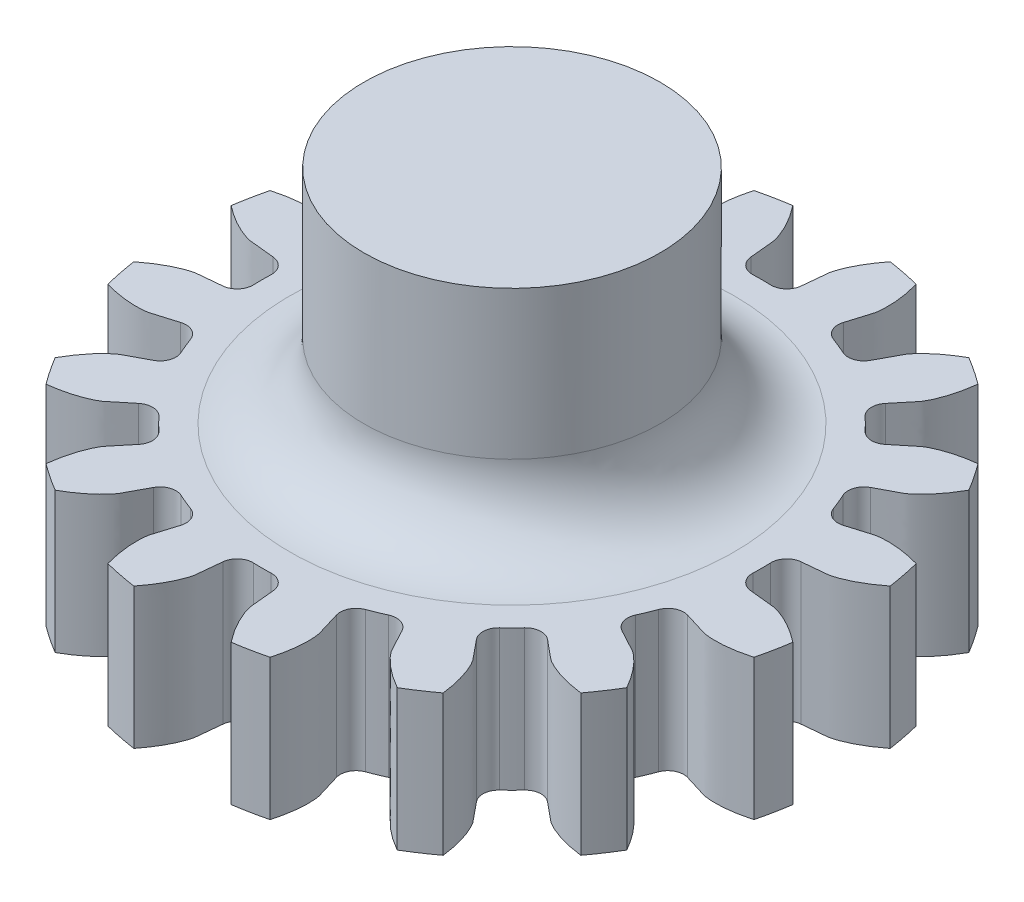
SolidWorks part; units mm, degrees
ref_plane "Front Plane" through (0, 0, 0) normal (0, 0, 1) x (1, 0, 0)
ref_plane "Top Plane" through (0, 0, 0) normal (0, 1, 0) x (1, 0, 0)
ref_plane "Right Plane" through (0, 0, 0) normal (1, 0, 0) x (0, 0, -1)
ref_plane "Plane1" through (0, -3.8, 0) normal (0, -1, 0) x (1, 0, 0)
sketch "Sketch1" plane through (0, -3.8, 0) normal (0, -1, 0) x (1, 0, 0)
  line L0 (1.32, -1.149) -> (-1.32, -1.149)
  arc A0 (-1.32, -1.149) -> (1.32, -1.149) centre (0, 0) cw
  arc A1 (7.1331, -0.679) -> (6.7458, -0.2386) centre (7.1726, -0.2537) cw
  arc A2 (6.7458, -0.2386) -> (6.7458, 0.2386) centre (0, 0) ccw
  arc A3 (6.7458, 0.2386) -> (7.1331, 0.679) centre (7.1726, 0.2537) cw
  arc A4 (8.9035, 1.3146) -> (8.7288, 2.1927) centre (0, 0) ccw
  arc A5 (6.8499, 2.1024) -> (6.3236, 2.3611) centre (6.7237, 2.5105) cw
  arc A6 (6.3236, 2.3611) -> (6.141, 2.8019) centre (0, 0) ccw
  arc A7 (6.141, 2.8019) -> (6.3303, 3.357) centre (6.5296, 2.9792) cw
  arc A8 (7.7227, 4.6217) -> (7.2253, 5.3661) centre (0, 0) ccw
  arc A9 (5.5239, 4.5638) -> (4.9387, 4.6013) centre (5.2512, 4.8924) cw
  arc A10 (4.9387, 4.6013) -> (4.6013, 4.9387) centre (0, 0) ccw
  arc A11 (4.6013, 4.9387) -> (4.5638, 5.5239) centre (4.8924, 5.2512) cw
  arc A12 (5.3661, 7.2253) -> (4.6217, 7.7227) centre (0, 0) ccw
  arc A13 (3.357, 6.3303) -> (2.8019, 6.141) centre (2.9792, 6.5296) cw
  arc A14 (2.8019, 6.141) -> (2.3611, 6.3236) centre (0, 0) ccw
  arc A15 (2.3611, 6.3236) -> (2.1024, 6.8499) centre (2.5105, 6.7237) cw
  arc A16 (2.1927, 8.7288) -> (1.3146, 8.9035) centre (0, 0) ccw
  arc A17 (0.679, 7.1331) -> (0.2386, 6.7458) centre (0.2537, 7.1726) cw
  arc A18 (0.2386, 6.7458) -> (-0.2386, 6.7458) centre (0, 0) ccw
  arc A19 (-0.2386, 6.7458) -> (-0.679, 7.1331) centre (-0.2537, 7.1726) cw
  arc A20 (-1.3146, 8.9035) -> (-2.1927, 8.7288) centre (0, 0) ccw
  arc A21 (-2.1024, 6.8499) -> (-2.3611, 6.3236) centre (-2.5105, 6.7237) cw
  arc A22 (-2.3611, 6.3236) -> (-2.8019, 6.141) centre (0, 0) ccw
  arc A23 (-2.8019, 6.141) -> (-3.357, 6.3303) centre (-2.9792, 6.5296) cw
  arc A24 (-4.6217, 7.7227) -> (-5.3661, 7.2253) centre (0, 0) ccw
  arc A25 (-4.5638, 5.5239) -> (-4.6013, 4.9387) centre (-4.8924, 5.2512) cw
  arc A26 (-4.6013, 4.9387) -> (-4.9387, 4.6013) centre (0, 0) ccw
  arc A27 (-4.9387, 4.6013) -> (-5.5239, 4.5638) centre (-5.2512, 4.8924) cw
  arc A28 (-7.2253, 5.3661) -> (-7.7227, 4.6217) centre (0, 0) ccw
  arc A29 (-6.3303, 3.357) -> (-6.141, 2.8019) centre (-6.5296, 2.9792) cw
  arc A30 (-6.141, 2.8019) -> (-6.3236, 2.3611) centre (0, 0) ccw
  arc A31 (-6.3236, 2.3611) -> (-6.8499, 2.1024) centre (-6.7237, 2.5105) cw
  arc A32 (-8.7288, 2.1927) -> (-8.9035, 1.3146) centre (0, 0) ccw
  arc A33 (-7.1331, 0.679) -> (-6.7458, 0.2386) centre (-7.1726, 0.2537) cw
  arc A34 (-6.7458, 0.2386) -> (-6.7458, -0.2386) centre (0, 0) ccw
  arc A35 (-6.7458, -0.2386) -> (-7.1331, -0.679) centre (-7.1726, -0.2537) cw
  arc A36 (-8.9035, -1.3146) -> (-8.7288, -2.1927) centre (0, 0) ccw
  arc A37 (-6.8499, -2.1024) -> (-6.3236, -2.3611) centre (-6.7237, -2.5105) cw
  arc A38 (-6.3236, -2.3611) -> (-6.141, -2.8019) centre (0, 0) ccw
  arc A39 (-6.141, -2.8019) -> (-6.3303, -3.357) centre (-6.5296, -2.9792) cw
  arc A40 (-7.7227, -4.6217) -> (-7.2253, -5.3661) centre (0, 0) ccw
  arc A41 (-5.5239, -4.5638) -> (-4.9387, -4.6013) centre (-5.2512, -4.8924) cw
  arc A42 (-4.9387, -4.6013) -> (-4.6013, -4.9387) centre (0, 0) ccw
  arc A43 (-4.6013, -4.9387) -> (-4.5638, -5.5239) centre (-4.8924, -5.2512) cw
  arc A44 (-5.3661, -7.2253) -> (-4.6217, -7.7227) centre (0, 0) ccw
  arc A45 (-3.357, -6.3303) -> (-2.8019, -6.141) centre (-2.9792, -6.5296) cw
  arc A46 (-2.8019, -6.141) -> (-2.3611, -6.3236) centre (0, 0) ccw
  arc A47 (-2.3611, -6.3236) -> (-2.1024, -6.8499) centre (-2.5105, -6.7237) cw
  arc A48 (-2.1927, -8.7288) -> (-1.3146, -8.9035) centre (0, 0) ccw
  arc A49 (-0.679, -7.1331) -> (-0.2386, -6.7458) centre (-0.2537, -7.1726) cw
  arc A50 (-0.2386, -6.7458) -> (0.2386, -6.7458) centre (0, 0) ccw
  arc A51 (0.2386, -6.7458) -> (0.679, -7.1331) centre (0.2537, -7.1726) cw
  arc A52 (1.3146, -8.9035) -> (2.1927, -8.7288) centre (0, 0) ccw
  arc A53 (2.1024, -6.8499) -> (2.3611, -6.3236) centre (2.5105, -6.7237) cw
  arc A54 (2.3611, -6.3236) -> (2.8019, -6.141) centre (0, 0) ccw
  arc A55 (2.8019, -6.141) -> (3.357, -6.3303) centre (2.9792, -6.5296) cw
  arc A56 (4.6217, -7.7227) -> (5.3661, -7.2253) centre (0, 0) ccw
  arc A57 (4.5638, -5.5239) -> (4.6013, -4.9387) centre (4.8924, -5.2512) cw
  arc A58 (4.6013, -4.9387) -> (4.9387, -4.6013) centre (0, 0) ccw
  arc A59 (4.9387, -4.6013) -> (5.5239, -4.5638) centre (5.2512, -4.8924) cw
  arc A60 (7.2253, -5.3661) -> (7.7227, -4.6217) centre (0, 0) ccw
  arc A61 (6.3303, -3.357) -> (6.141, -2.8019) centre (6.5296, -2.9792) cw
  arc A62 (6.141, -2.8019) -> (6.3236, -2.3611) centre (0, 0) ccw
  arc A63 (6.3236, -2.3611) -> (6.8499, -2.1024) centre (6.7237, -2.5105) cw
  arc A64 (8.7288, -2.1927) -> (8.9035, -1.3146) centre (0, 0) ccw
  spline S0 degree 3 poles (7.1331, -0.679) (7.4618, -0.7095) (7.7948, -0.7412) (7.8257, -0.7485) (7.8795, -0.7599) (7.9434, -0.7779) (8.0276, -0.8057) (8.1278, -0.8446) (8.244, -0.8965) (8.3748, -0.963) (8.5191, -1.0456) (8.6757, -1.1461) (8.8054, -1.2381) (8.8825, -1.298) (8.9035, -1.3146) knots 0.061706 0.061706 0.061706 0.061706 0.215819 0.251311 0.29713 0.351345 0.412818 0.480779 0.55466 0.634022 0.718508 0.807827 0.901728 0.93689 0.93689 0.93689 0.93689
  spline S1 degree 3 poles (7.1331, 0.679) (7.4618, 0.7095) (7.7948, 0.7412) (7.8257, 0.7485) (7.8795, 0.7599) (7.9434, 0.7779) (8.0276, 0.8057) (8.1278, 0.8446) (8.244, 0.8965) (8.3748, 0.963) (8.5191, 1.0456) (8.6757, 1.1461) (8.8054, 1.2381) (8.8825, 1.298) (8.9035, 1.3146) knots 0.061706 0.061706 0.061706 0.061706 0.215819 0.251311 0.29713 0.351345 0.412818 0.480779 0.55466 0.634022 0.718508 0.807827 0.901728 0.93689 0.93689 0.93689 0.93689
  spline S2 degree 3 poles (6.8499, 2.1024) (7.1654, 2.2) (7.485, 2.2982) (7.5165, 2.3032) (7.5705, 2.3133) (7.6364, 2.3211) (7.7249, 2.3277) (7.8323, 2.33) (7.9595, 2.3266) (8.1058, 2.3152) (8.2708, 2.2942) (8.4539, 2.2612) (8.6089, 2.2258) (8.7031, 2.2) (8.7288, 2.1927) knots 0.061706 0.061706 0.061706 0.061706 0.215819 0.251311 0.29713 0.351345 0.412818 0.480779 0.55466 0.634022 0.718508 0.807827 0.901728 0.93689 0.93689 0.93689 0.93689
  spline S3 degree 3 poles (6.3303, 3.357) (6.6223, 3.511) (6.9178, 3.6677) (6.9436, 3.6863) (6.9889, 3.7174) (7.041, 3.7585) (7.1083, 3.8164) (7.1859, 3.8907) (7.2734, 3.9831) (7.3688, 4.0946) (7.4705, 4.2261) (7.5767, 4.3789) (7.6613, 4.5136) (7.7096, 4.5984) (7.7227, 4.6217) knots 0.061706 0.061706 0.061706 0.061706 0.215819 0.251311 0.29713 0.351345 0.412818 0.480779 0.55466 0.634022 0.718508 0.807827 0.901728 0.93689 0.93689 0.93689 0.93689
  spline S4 degree 3 poles (5.5239, 4.5638) (5.778, 4.7746) (6.0358, 4.9876) (6.0629, 5.0043) (6.109, 5.0343) (6.1669, 5.0667) (6.2461, 5.1067) (6.3444, 5.15) (6.4633, 5.1955) (6.6028, 5.241) (6.7633, 5.2846) (6.945, 5.3242) (7.1018, 5.3509) (7.1987, 5.363) (7.2253, 5.3661) knots 0.061706 0.061706 0.061706 0.061706 0.215819 0.251311 0.29713 0.351345 0.412818 0.480779 0.55466 0.634022 0.718508 0.807827 0.901728 0.93689 0.93689 0.93689 0.93689
  spline S5 degree 3 poles (4.5638, 5.5239) (4.7746, 5.778) (4.9876, 6.0358) (5.0043, 6.0629) (5.0343, 6.109) (5.0667, 6.1669) (5.1067, 6.2461) (5.15, 6.3444) (5.1955, 6.4633) (5.241, 6.6028) (5.2846, 6.7633) (5.3242, 6.945) (5.3509, 7.1018) (5.363, 7.1987) (5.3661, 7.2253) knots 0.061706 0.061706 0.061706 0.061706 0.215819 0.251311 0.29713 0.351345 0.412818 0.480779 0.55466 0.634022 0.718508 0.807827 0.901728 0.93689 0.93689 0.93689 0.93689
  spline S6 degree 3 poles (3.357, 6.3303) (3.511, 6.6223) (3.6677, 6.9178) (3.6863, 6.9436) (3.7174, 6.9889) (3.7585, 7.041) (3.8164, 7.1083) (3.8907, 7.1859) (3.9831, 7.2734) (4.0946, 7.3688) (4.2261, 7.4705) (4.3789, 7.5767) (4.5136, 7.6613) (4.5984, 7.7096) (4.6217, 7.7227) knots 0.061706 0.061706 0.061706 0.061706 0.215819 0.251311 0.29713 0.351345 0.412818 0.480779 0.55466 0.634022 0.718508 0.807827 0.901728 0.93689 0.93689 0.93689 0.93689
  spline S7 degree 3 poles (2.1024, 6.8499) (2.2, 7.1654) (2.2982, 7.485) (2.3032, 7.5165) (2.3133, 7.5705) (2.3211, 7.6364) (2.3277, 7.7249) (2.33, 7.8323) (2.3266, 7.9595) (2.3152, 8.1058) (2.2942, 8.2708) (2.2612, 8.4539) (2.2258, 8.6089) (2.2, 8.7031) (2.1927, 8.7288) knots 0.061706 0.061706 0.061706 0.061706 0.215819 0.251311 0.29713 0.351345 0.412818 0.480779 0.55466 0.634022 0.718508 0.807827 0.901728 0.93689 0.93689 0.93689 0.93689
  spline S8 degree 3 poles (0.679, 7.1331) (0.7095, 7.4618) (0.7412, 7.7948) (0.7485, 7.8257) (0.7599, 7.8795) (0.7779, 7.9434) (0.8057, 8.0276) (0.8446, 8.1278) (0.8965, 8.244) (0.963, 8.3748) (1.0456, 8.5191) (1.1461, 8.6757) (1.2381, 8.8054) (1.298, 8.8825) (1.3146, 8.9035) knots 0.061706 0.061706 0.061706 0.061706 0.215819 0.251311 0.29713 0.351345 0.412818 0.480779 0.55466 0.634022 0.718508 0.807827 0.901728 0.93689 0.93689 0.93689 0.93689
  spline S9 degree 3 poles (-0.679, 7.1331) (-0.7095, 7.4618) (-0.7412, 7.7948) (-0.7485, 7.8257) (-0.7599, 7.8795) (-0.7779, 7.9434) (-0.8057, 8.0276) (-0.8446, 8.1278) (-0.8965, 8.244) (-0.963, 8.3748) (-1.0456, 8.5191) (-1.1461, 8.6757) (-1.2381, 8.8054) (-1.298, 8.8825) (-1.3146, 8.9035) knots 0.061706 0.061706 0.061706 0.061706 0.215819 0.251311 0.29713 0.351345 0.412818 0.480779 0.55466 0.634022 0.718508 0.807827 0.901728 0.93689 0.93689 0.93689 0.93689
  spline S10 degree 3 poles (-2.1024, 6.8499) (-2.2, 7.1654) (-2.2982, 7.485) (-2.3032, 7.5165) (-2.3133, 7.5705) (-2.3211, 7.6364) (-2.3277, 7.7249) (-2.33, 7.8323) (-2.3266, 7.9595) (-2.3152, 8.1058) (-2.2942, 8.2708) (-2.2612, 8.4539) (-2.2258, 8.6089) (-2.2, 8.7031) (-2.1927, 8.7288) knots 0.061706 0.061706 0.061706 0.061706 0.215819 0.251311 0.29713 0.351345 0.412818 0.480779 0.55466 0.634022 0.718508 0.807827 0.901728 0.93689 0.93689 0.93689 0.93689
  spline S11 degree 3 poles (-3.357, 6.3303) (-3.511, 6.6223) (-3.6677, 6.9178) (-3.6863, 6.9436) (-3.7174, 6.9889) (-3.7585, 7.041) (-3.8164, 7.1083) (-3.8907, 7.1859) (-3.9831, 7.2734) (-4.0946, 7.3688) (-4.2261, 7.4705) (-4.3789, 7.5767) (-4.5136, 7.6613) (-4.5984, 7.7096) (-4.6217, 7.7227) knots 0.061706 0.061706 0.061706 0.061706 0.215819 0.251311 0.29713 0.351345 0.412818 0.480779 0.55466 0.634022 0.718508 0.807827 0.901728 0.93689 0.93689 0.93689 0.93689
  spline S12 degree 3 poles (-4.5638, 5.5239) (-4.7746, 5.778) (-4.9876, 6.0358) (-5.0043, 6.0629) (-5.0343, 6.109) (-5.0667, 6.1669) (-5.1067, 6.2461) (-5.15, 6.3444) (-5.1955, 6.4633) (-5.241, 6.6028) (-5.2846, 6.7633) (-5.3242, 6.945) (-5.3509, 7.1018) (-5.363, 7.1987) (-5.3661, 7.2253) knots 0.061706 0.061706 0.061706 0.061706 0.215819 0.251311 0.29713 0.351345 0.412818 0.480779 0.55466 0.634022 0.718508 0.807827 0.901728 0.93689 0.93689 0.93689 0.93689
  spline S13 degree 3 poles (-5.5239, 4.5638) (-5.778, 4.7746) (-6.0358, 4.9876) (-6.0629, 5.0043) (-6.109, 5.0343) (-6.1669, 5.0667) (-6.2461, 5.1067) (-6.3444, 5.15) (-6.4633, 5.1955) (-6.6028, 5.241) (-6.7633, 5.2846) (-6.945, 5.3242) (-7.1018, 5.3509) (-7.1987, 5.363) (-7.2253, 5.3661) knots 0.061706 0.061706 0.061706 0.061706 0.215819 0.251311 0.29713 0.351345 0.412818 0.480779 0.55466 0.634022 0.718508 0.807827 0.901728 0.93689 0.93689 0.93689 0.93689
  spline S14 degree 3 poles (-6.3303, 3.357) (-6.6223, 3.511) (-6.9178, 3.6677) (-6.9436, 3.6863) (-6.9889, 3.7174) (-7.041, 3.7585) (-7.1083, 3.8164) (-7.1859, 3.8907) (-7.2734, 3.9831) (-7.3688, 4.0946) (-7.4705, 4.2261) (-7.5767, 4.3789) (-7.6613, 4.5136) (-7.7096, 4.5984) (-7.7227, 4.6217) knots 0.061706 0.061706 0.061706 0.061706 0.215819 0.251311 0.29713 0.351345 0.412818 0.480779 0.55466 0.634022 0.718508 0.807827 0.901728 0.93689 0.93689 0.93689 0.93689
  spline S15 degree 3 poles (-6.8499, 2.1024) (-7.1654, 2.2) (-7.485, 2.2982) (-7.5165, 2.3032) (-7.5705, 2.3133) (-7.6364, 2.3211) (-7.7249, 2.3277) (-7.8323, 2.33) (-7.9595, 2.3266) (-8.1058, 2.3152) (-8.2708, 2.2942) (-8.4539, 2.2612) (-8.6089, 2.2258) (-8.7031, 2.2) (-8.7288, 2.1927) knots 0.061706 0.061706 0.061706 0.061706 0.215819 0.251311 0.29713 0.351345 0.412818 0.480779 0.55466 0.634022 0.718508 0.807827 0.901728 0.93689 0.93689 0.93689 0.93689
  spline S16 degree 3 poles (-7.1331, 0.679) (-7.4618, 0.7095) (-7.7948, 0.7412) (-7.8257, 0.7485) (-7.8795, 0.7599) (-7.9434, 0.7779) (-8.0276, 0.8057) (-8.1278, 0.8446) (-8.244, 0.8965) (-8.3748, 0.963) (-8.5191, 1.0456) (-8.6757, 1.1461) (-8.8054, 1.2381) (-8.8825, 1.298) (-8.9035, 1.3146) knots 0.061706 0.061706 0.061706 0.061706 0.215819 0.251311 0.29713 0.351345 0.412818 0.480779 0.55466 0.634022 0.718508 0.807827 0.901728 0.93689 0.93689 0.93689 0.93689
  spline S17 degree 3 poles (-7.1331, -0.679) (-7.4618, -0.7095) (-7.7948, -0.7412) (-7.8257, -0.7485) (-7.8795, -0.7599) (-7.9434, -0.7779) (-8.0276, -0.8057) (-8.1278, -0.8446) (-8.244, -0.8965) (-8.3748, -0.963) (-8.5191, -1.0456) (-8.6757, -1.1461) (-8.8054, -1.2381) (-8.8825, -1.298) (-8.9035, -1.3146) knots 0.061706 0.061706 0.061706 0.061706 0.215819 0.251311 0.29713 0.351345 0.412818 0.480779 0.55466 0.634022 0.718508 0.807827 0.901728 0.93689 0.93689 0.93689 0.93689
  spline S18 degree 3 poles (-6.8499, -2.1024) (-7.1654, -2.2) (-7.485, -2.2982) (-7.5165, -2.3032) (-7.5705, -2.3133) (-7.6364, -2.3211) (-7.7249, -2.3277) (-7.8323, -2.33) (-7.9595, -2.3266) (-8.1058, -2.3152) (-8.2708, -2.2942) (-8.4539, -2.2612) (-8.6089, -2.2258) (-8.7031, -2.2) (-8.7288, -2.1927) knots 0.061706 0.061706 0.061706 0.061706 0.215819 0.251311 0.29713 0.351345 0.412818 0.480779 0.55466 0.634022 0.718508 0.807827 0.901728 0.93689 0.93689 0.93689 0.93689
  spline S19 degree 3 poles (-6.3303, -3.357) (-6.6223, -3.511) (-6.9178, -3.6677) (-6.9436, -3.6863) (-6.9889, -3.7174) (-7.041, -3.7585) (-7.1083, -3.8164) (-7.1859, -3.8907) (-7.2734, -3.9831) (-7.3688, -4.0946) (-7.4705, -4.2261) (-7.5767, -4.3789) (-7.6613, -4.5136) (-7.7096, -4.5984) (-7.7227, -4.6217) knots 0.061706 0.061706 0.061706 0.061706 0.215819 0.251311 0.29713 0.351345 0.412818 0.480779 0.55466 0.634022 0.718508 0.807827 0.901728 0.93689 0.93689 0.93689 0.93689
  spline S20 degree 3 poles (-5.5239, -4.5638) (-5.778, -4.7746) (-6.0358, -4.9876) (-6.0629, -5.0043) (-6.109, -5.0343) (-6.1669, -5.0667) (-6.2461, -5.1067) (-6.3444, -5.15) (-6.4633, -5.1955) (-6.6028, -5.241) (-6.7633, -5.2846) (-6.945, -5.3242) (-7.1018, -5.3509) (-7.1987, -5.363) (-7.2253, -5.3661) knots 0.061706 0.061706 0.061706 0.061706 0.215819 0.251311 0.29713 0.351345 0.412818 0.480779 0.55466 0.634022 0.718508 0.807827 0.901728 0.93689 0.93689 0.93689 0.93689
  spline S21 degree 3 poles (-4.5638, -5.5239) (-4.7746, -5.778) (-4.9876, -6.0358) (-5.0043, -6.0629) (-5.0343, -6.109) (-5.0667, -6.1669) (-5.1067, -6.2461) (-5.15, -6.3444) (-5.1955, -6.4633) (-5.241, -6.6028) (-5.2846, -6.7633) (-5.3242, -6.945) (-5.3509, -7.1018) (-5.363, -7.1987) (-5.3661, -7.2253) knots 0.061706 0.061706 0.061706 0.061706 0.215819 0.251311 0.29713 0.351345 0.412818 0.480779 0.55466 0.634022 0.718508 0.807827 0.901728 0.93689 0.93689 0.93689 0.93689
  spline S22 degree 3 poles (-3.357, -6.3303) (-3.511, -6.6223) (-3.6677, -6.9178) (-3.6863, -6.9436) (-3.7174, -6.9889) (-3.7585, -7.041) (-3.8164, -7.1083) (-3.8907, -7.1859) (-3.9831, -7.2734) (-4.0946, -7.3688) (-4.2261, -7.4705) (-4.3789, -7.5767) (-4.5136, -7.6613) (-4.5984, -7.7096) (-4.6217, -7.7227) knots 0.061706 0.061706 0.061706 0.061706 0.215819 0.251311 0.29713 0.351345 0.412818 0.480779 0.55466 0.634022 0.718508 0.807827 0.901728 0.93689 0.93689 0.93689 0.93689
  spline S23 degree 3 poles (-2.1024, -6.8499) (-2.2, -7.1654) (-2.2982, -7.485) (-2.3032, -7.5165) (-2.3133, -7.5705) (-2.3211, -7.6364) (-2.3277, -7.7249) (-2.33, -7.8323) (-2.3266, -7.9595) (-2.3152, -8.1058) (-2.2942, -8.2708) (-2.2612, -8.4539) (-2.2258, -8.6089) (-2.2, -8.7031) (-2.1927, -8.7288) knots 0.061706 0.061706 0.061706 0.061706 0.215819 0.251311 0.29713 0.351345 0.412818 0.480779 0.55466 0.634022 0.718508 0.807827 0.901728 0.93689 0.93689 0.93689 0.93689
  spline S24 degree 3 poles (-0.679, -7.1331) (-0.7095, -7.4618) (-0.7412, -7.7948) (-0.7485, -7.8257) (-0.7599, -7.8795) (-0.7779, -7.9434) (-0.8057, -8.0276) (-0.8446, -8.1278) (-0.8965, -8.244) (-0.963, -8.3748) (-1.0456, -8.5191) (-1.1461, -8.6757) (-1.2381, -8.8054) (-1.298, -8.8825) (-1.3146, -8.9035) knots 0.061706 0.061706 0.061706 0.061706 0.215819 0.251311 0.29713 0.351345 0.412818 0.480779 0.55466 0.634022 0.718508 0.807827 0.901728 0.93689 0.93689 0.93689 0.93689
  spline S25 degree 3 poles (0.679, -7.1331) (0.7095, -7.4618) (0.7412, -7.7948) (0.7485, -7.8257) (0.7599, -7.8795) (0.7779, -7.9434) (0.8057, -8.0276) (0.8446, -8.1278) (0.8965, -8.244) (0.963, -8.3748) (1.0456, -8.5191) (1.1461, -8.6757) (1.2381, -8.8054) (1.298, -8.8825) (1.3146, -8.9035) knots 0.061706 0.061706 0.061706 0.061706 0.215819 0.251311 0.29713 0.351345 0.412818 0.480779 0.55466 0.634022 0.718508 0.807827 0.901728 0.93689 0.93689 0.93689 0.93689
  spline S26 degree 3 poles (2.1024, -6.8499) (2.2, -7.1654) (2.2982, -7.485) (2.3032, -7.5165) (2.3133, -7.5705) (2.3211, -7.6364) (2.3277, -7.7249) (2.33, -7.8323) (2.3266, -7.9595) (2.3152, -8.1058) (2.2942, -8.2708) (2.2612, -8.4539) (2.2258, -8.6089) (2.2, -8.7031) (2.1927, -8.7288) knots 0.061706 0.061706 0.061706 0.061706 0.215819 0.251311 0.29713 0.351345 0.412818 0.480779 0.55466 0.634022 0.718508 0.807827 0.901728 0.93689 0.93689 0.93689 0.93689
  spline S27 degree 3 poles (3.357, -6.3303) (3.511, -6.6223) (3.6677, -6.9178) (3.6863, -6.9436) (3.7174, -6.9889) (3.7585, -7.041) (3.8164, -7.1083) (3.8907, -7.1859) (3.9831, -7.2734) (4.0946, -7.3688) (4.2261, -7.4705) (4.3789, -7.5767) (4.5136, -7.6613) (4.5984, -7.7096) (4.6217, -7.7227) knots 0.061706 0.061706 0.061706 0.061706 0.215819 0.251311 0.29713 0.351345 0.412818 0.480779 0.55466 0.634022 0.718508 0.807827 0.901728 0.93689 0.93689 0.93689 0.93689
  spline S28 degree 3 poles (4.5638, -5.5239) (4.7746, -5.778) (4.9876, -6.0358) (5.0043, -6.0629) (5.0343, -6.109) (5.0667, -6.1669) (5.1067, -6.2461) (5.15, -6.3444) (5.1955, -6.4633) (5.241, -6.6028) (5.2846, -6.7633) (5.3242, -6.945) (5.3509, -7.1018) (5.363, -7.1987) (5.3661, -7.2253) knots 0.061706 0.061706 0.061706 0.061706 0.215819 0.251311 0.29713 0.351345 0.412818 0.480779 0.55466 0.634022 0.718508 0.807827 0.901728 0.93689 0.93689 0.93689 0.93689
  spline S29 degree 3 poles (5.5239, -4.5638) (5.778, -4.7746) (6.0358, -4.9876) (6.0629, -5.0043) (6.109, -5.0343) (6.1669, -5.0667) (6.2461, -5.1067) (6.3444, -5.15) (6.4633, -5.1955) (6.6028, -5.241) (6.7633, -5.2846) (6.945, -5.3242) (7.1018, -5.3509) (7.1987, -5.363) (7.2253, -5.3661) knots 0.061706 0.061706 0.061706 0.061706 0.215819 0.251311 0.29713 0.351345 0.412818 0.480779 0.55466 0.634022 0.718508 0.807827 0.901728 0.93689 0.93689 0.93689 0.93689
  spline S30 degree 3 poles (6.3303, -3.357) (6.6223, -3.511) (6.9178, -3.6677) (6.9436, -3.6863) (6.9889, -3.7174) (7.041, -3.7585) (7.1083, -3.8164) (7.1859, -3.8907) (7.2734, -3.9831) (7.3688, -4.0946) (7.4705, -4.2261) (7.5767, -4.3789) (7.6613, -4.5136) (7.7096, -4.5984) (7.7227, -4.6217) knots 0.061706 0.061706 0.061706 0.061706 0.215819 0.251311 0.29713 0.351345 0.412818 0.480779 0.55466 0.634022 0.718508 0.807827 0.901728 0.93689 0.93689 0.93689 0.93689
  spline S31 degree 3 poles (6.8499, -2.1024) (7.1654, -2.2) (7.485, -2.2982) (7.5165, -2.3032) (7.5705, -2.3133) (7.6364, -2.3211) (7.7249, -2.3277) (7.8323, -2.33) (7.9595, -2.3266) (8.1058, -2.3152) (8.2708, -2.2942) (8.4539, -2.2612) (8.6089, -2.2258) (8.7031, -2.2) (8.7288, -2.1927) knots 0.061706 0.061706 0.061706 0.061706 0.215819 0.251311 0.29713 0.351345 0.412818 0.480779 0.55466 0.634022 0.718508 0.807827 0.901728 0.93689 0.93689 0.93689 0.93689
extrude "Boss-Extrude1" add sketch "Sketch1" against normal blind 3.8
sketch "Sketch2" plane through (0, 0, 0) normal (0, 1, 0) x (1, 0, 0)
  circle A0 centre (0, 0) radius 4
  circle A1 centre (0, 0) radius 1.75
  dimension "D1" = 8
  dimension "D2" = 3.5
extrude "Boss-Extrude2" add sketch "Sketch2" along normal blind 6
sketch "Sketch3" plane through (0, 6, 0) normal (0, 1, 0) x (1, 0, 0)
  circle A0 centre (0, 0) radius 4
extrude "Boss-Extrude3" add sketch "Sketch3" against normal blind 0.5
fillet "Fillet1" radius 2 1 edges at (0, 0, -4)
